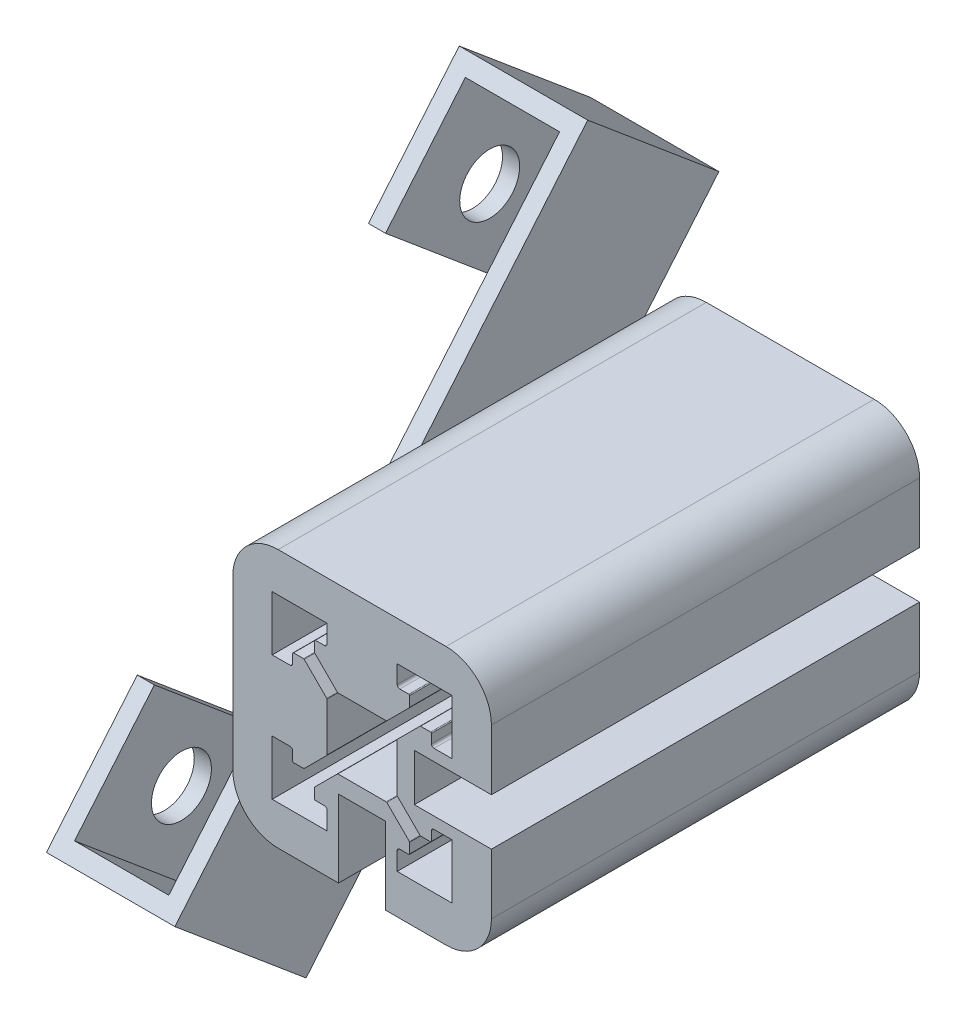
SolidWorks part; units mm, degrees
ref_plane "Ön Düzlem" through (0, 0, 0) normal (0, 0, 1) x (1, 0, 0)
ref_plane "Üst Düzlem" through (0, 0, 0) normal (0, 1, 0) x (1, 0, 0)
ref_plane "Sağ Düzlem" through (0, 0, 0) normal (1, 0, 0) x (0, 0, -1)
sketch "Çizim6" plane through (0, 0, 0) normal (0, 0, 1) x (1, 0, 0)
  line L5 (-115.3715, 18.9738) -> (-110.3715, 18.9738)
  line L6 (-115.3715, 13.4738) -> (-110.3715, 13.4738)
  line L64 (-135.0715, 20.3238) -> (-133.8715, 20.3238)
  line L65 (-133.5715, 20.6238) -> (-133.5715, 21.6738)
  line L66 (-133.4715, 21.7738) -> (-132.3044, 21.7738)
  line L67 (-132.2336, 21.7445) -> (-129.6008, 19.1116)
  line L68 (-129.5715, 19.0409) -> (-129.5715, 13.4066)
  line L69 (-132.2336, 10.7031) -> (-129.6008, 13.3359)
  line L70 (-133.4715, 10.6738) -> (-132.3044, 10.6738)
  line L71 (-133.5715, 11.8238) -> (-133.5715, 10.7738)
  line L72 (-135.0715, 12.1238) -> (-133.8715, 12.1238)
  line L79 (-129.5715, 6.6238) -> (-129.5715, 7.8238)
  line L80 (-129.8715, 8.1238) -> (-130.9215, 8.1238)
  line L81 (-131.0215, 8.2238) -> (-131.0215, 9.3909)
  line L82 (-130.9922, 9.4616) -> (-128.3594, 12.0945)
  line L83 (-128.2887, 12.1238) -> (-122.6544, 12.1238)
  line L84 (-119.9508, 9.4616) -> (-122.5836, 12.0945)
  line L85 (-119.9215, 8.2238) -> (-119.9215, 9.3909)
  line L86 (-121.0715, 8.1238) -> (-120.0215, 8.1238)
  line L87 (-121.3715, 6.6238) -> (-121.3715, 7.8238)
  line L94 (-115.8715, 12.1238) -> (-117.0715, 12.1238)
  line L95 (-117.3715, 11.8238) -> (-117.3715, 10.7738)
  line L96 (-117.4715, 10.6738) -> (-118.6387, 10.6738)
  line L97 (-118.7094, 10.7031) -> (-121.3422, 13.3359)
  line L98 (-121.3715, 13.4066) -> (-121.3715, 19.0409)
  line L99 (-118.7094, 21.7445) -> (-121.3422, 19.1116)
  line L100 (-117.4715, 21.7738) -> (-118.6387, 21.7738)
  line L101 (-117.3715, 20.6238) -> (-117.3715, 21.6738)
  line L102 (-115.8715, 20.3238) -> (-117.0715, 20.3238)
  line L109 (-121.3715, 25.8238) -> (-121.3715, 24.6238)
  line L110 (-121.0715, 24.3238) -> (-120.0215, 24.3238)
  line L111 (-119.9215, 24.2238) -> (-119.9215, 23.0566)
  line L112 (-119.9508, 22.9859) -> (-122.5836, 20.3531)
  line L113 (-122.6544, 20.3238) -> (-128.2887, 20.3238)
  line L114 (-130.9922, 22.9859) -> (-128.3594, 20.3531)
  line L115 (-131.0215, 24.2238) -> (-131.0215, 23.0566)
  line L116 (-129.8715, 24.3238) -> (-130.9215, 24.3238)
  line L117 (-129.5715, 25.8238) -> (-129.5715, 24.6238)
  line L122 (-119.3715, 18.9738) -> (-115.3715, 18.9738)
  line L123 (-119.3715, 13.4738) -> (-115.3715, 13.4738)
  line L126 (-119.3715, 18.9738) -> (-119.3715, 13.4738)
  line L128 (-122.7215, 10.1238) -> (-122.7215, 6.1238)
  line L129 (-122.7215, 10.1238) -> (-128.2215, 10.1238)
  line L130 (-128.2215, 10.1238) -> (-128.2215, 6.1238)
  line L142 (-135.0715, 20.3238) -> (-135.8715, 20.3238)
  line L143 (-135.0715, 12.1238) -> (-135.5715, 12.1238)
  line L144 (-129.5715, 6.6238) -> (-129.5715, 6.1238)
  line L145 (-129.5715, 25.8238) -> (-129.5715, 26.6238)
  line L146 (-121.3715, 25.8238) -> (-121.3715, 26.3238)
  line L147 (-115.8715, 20.3238) -> (-115.3715, 20.3238)
  line L148 (-115.8715, 12.1238) -> (-115.3715, 12.1238)
  line L149 (-121.3715, 6.6238) -> (-121.3715, 6.1238)
  line L150 (-135.2715, 31.3238) -> (-130.0215, 31.3238)
  line L151 (-130.0215, 31.3238) -> (-128.2215, 31.3238)
  line L152 (-125.4715, 31.3238) -> (-125.4715, 31.3238)
  line L153 (-125.4715, 31.3238) -> (-125.4715, 31.3238)
  line L154 (-125.4715, 31.3238) -> (-125.4715, 31.3238)
  line L155 (-120.9215, 31.3238) -> (-122.7215, 31.3238)
  line L156 (-120.9215, 31.3238) -> (-115.6715, 31.3238)
  line L157 (-110.3715, 20.7738) -> (-110.3715, 26.0238)
  line L158 (-110.3715, 20.7738) -> (-110.3715, 18.9738)
  line L159 (-110.3715, 16.2238) -> (-110.3715, 16.2238)
  line L160 (-110.3715, 16.2238) -> (-110.3715, 16.2238)
  line L161 (-110.3715, 16.2238) -> (-110.3715, 16.2238)
  line L162 (-110.3715, 11.6738) -> (-110.3715, 13.4738)
  line L163 (-110.3715, 6.4238) -> (-110.3715, 11.6738)
  line L164 (-120.9215, 1.1238) -> (-115.6715, 1.1238)
  line L165 (-120.9215, 1.1238) -> (-122.7215, 1.1238)
  line L166 (-125.4715, 1.1238) -> (-125.4715, 1.1238)
  line L167 (-125.4715, 1.1238) -> (-125.4715, 1.1238)
  line L168 (-125.4715, 1.1238) -> (-125.4715, 1.1238)
  line L169 (-130.0215, 1.1238) -> (-128.2215, 1.1238)
  line L170 (-135.2715, 1.1238) -> (-130.0215, 1.1238)
  line L171 (-140.5715, 6.4238) -> (-140.5715, 11.6738)
  line L172 (-140.5715, 11.6738) -> (-140.5715, 16.2238)
  line L173 (-140.5715, 16.2238) -> (-140.5715, 16.2238)
  line L174 (-140.5715, 16.2238) -> (-140.5715, 16.2238)
  line L175 (-140.5715, 16.2238) -> (-140.5715, 16.2238)
  line L176 (-140.5715, 20.7738) -> (-140.5715, 16.2238)
  line L177 (-140.5715, 20.7738) -> (-140.5715, 26.0238)
  line L178 (-135.5715, 20.7738) -> (-135.5715, 26.0238) construction
  line L179 (-135.2715, 26.3238) -> (-130.0215, 26.3238) construction
  line L180 (-115.3715, 20.7738) -> (-115.3715, 26.0238) construction
  line L181 (-120.9215, 26.3238) -> (-115.6715, 26.3238) construction
  line L182 (-115.3715, 20.7738) -> (-115.3715, 18.9738) construction
  line L183 (-115.3715, 6.4238) -> (-115.3715, 11.6738) construction
  line L184 (-120.9215, 6.1238) -> (-115.6715, 6.1238) construction
  line L185 (-115.3715, 11.6738) -> (-115.3715, 13.4738) construction
  line L186 (-120.9215, 6.1238) -> (-122.7215, 6.1238) construction
  line L187 (-120.9215, 26.3238) -> (-122.7215, 26.3238) construction
  line L188 (-130.0215, 26.3238) -> (-128.2215, 26.3238) construction
  line L189 (-135.5715, 20.7738) -> (-135.5715, 18.9738) construction
  line L190 (-135.5715, 11.6738) -> (-135.5715, 13.4738) construction
  line L191 (-135.5715, 6.4238) -> (-135.5715, 11.6738) construction
  line L192 (-135.2715, 6.1238) -> (-130.0215, 6.1238) construction
  line L193 (-130.0215, 6.1238) -> (-128.2215, 6.1238) construction
  line L194 (-122.7215, 6.1238) -> (-122.7215, 1.1238)
  line L195 (-128.2215, 6.1238) -> (-128.2215, 1.1238)
  line L196 (-135.8715, 20.3238) -> (-135.9715, 20.3238)
  line L197 (-135.9715, 20.2238) -> (-135.9715, 26.7238) construction
  line L198 (-122.7215, 31.3238) -> (-128.2215, 31.3238)
  line L204 (-110.3715, 20.7738) -> (-110.3715, 16.2238) construction
  line L205 (-110.3715, 11.6738) -> (-110.3715, 16.2238) construction
  line L206 (-120.9215, 31.3238) -> (-125.4715, 31.3238) construction
  line L207 (-130.0215, 31.3238) -> (-125.4715, 31.3238) construction
  line L208 (-120.9215, 1.1238) -> (-125.4715, 1.1238) construction
  line L209 (-130.0215, 1.1238) -> (-125.4715, 1.1238) construction
  line L210 (-131.5715, 13.4738) -> (-135.5715, 13.4738) [skipped]
  line L211 (-131.5715, 13.4738) -> (-135.5715, 13.4738) construction
  line L212 (-131.5715, 13.4738) -> (-131.5715, 18.9738) [skipped]
  line L213 (-131.5715, 13.4738) -> (-131.5715, 18.9738) construction
  line L214 (-131.5715, 18.9738) -> (-135.5715, 18.9738) [skipped]
  line L215 (-131.5715, 18.9738) -> (-135.5715, 18.9738) construction
  line L216 (-129.5715, 26.6238) -> (-129.5715, 26.7238)
  line L217 (-135.9715, 26.7238) -> (-129.4715, 26.7238) construction
  line L218 (-114.9715, 26.7238) -> (-114.9715, 20.3238)
  line L219 (-121.3715, 26.7238) -> (-114.9715, 26.7238)
  line L220 (-114.9715, 5.7238) -> (-121.3715, 5.7238)
  line L221 (-114.9715, 12.1238) -> (-114.9715, 5.7238)
  line L222 (-135.9715, 5.7238) -> (-135.9715, 12.1238)
  line L223 (-129.5715, 5.7238) -> (-135.9715, 5.7238)
  line L224 (-121.3715, 6.1238) -> (-121.3715, 5.7238)
  line L225 (-115.3715, 12.1238) -> (-114.9715, 12.1238)
  line L226 (-129.5715, 6.1238) -> (-129.5715, 5.7238)
  line L227 (-135.9715, 20.3238) -> (-135.9715, 26.7238)
  line L228 (-135.9715, 26.7238) -> (-129.5715, 26.7238)
  line L229 (-135.5715, 12.1238) -> (-135.9715, 12.1238)
  line L230 (-121.3715, 26.3238) -> (-121.3715, 26.7238)
  line L231 (-115.3715, 20.3238) -> (-114.9715, 20.3238)
  line L240 (-121.4715, 25.8238) -> (-121.4715, 26.3238) construction
  line L241 (-121.4715, 25.8238) -> (-121.4715, 24.6238) construction
  line L242 (-121.0715, 24.2238) -> (-120.0215, 24.2238) construction
  line L243 (-120.0215, 24.2238) -> (-120.0215, 23.0566) construction
  line L244 (-120.0215, 23.0566) -> (-122.6544, 20.4238) construction
  line L245 (-122.6544, 20.4238) -> (-128.2887, 20.4238) construction
  line L246 (-130.9215, 23.0566) -> (-128.2887, 20.4238) construction
  line L247 (-130.9215, 24.2238) -> (-130.9215, 23.0566) construction
  line L248 (-129.8715, 24.2238) -> (-130.9215, 24.2238) construction
  line L249 (-129.4715, 25.8238) -> (-129.4715, 24.6238) construction
  line L250 (-129.4715, 25.8238) -> (-129.4715, 26.7238) construction
  line L251 (-135.8715, 26.6238) -> (-129.5715, 26.6238) construction
  line L252 (-135.8715, 20.3238) -> (-135.8715, 26.6238) construction
  line L253 (-135.0715, 20.2238) -> (-135.9715, 20.2238) construction
  line L254 (-135.0715, 20.2238) -> (-133.8715, 20.2238) construction
  line L255 (-133.4715, 20.6238) -> (-133.4715, 21.6738) construction
  line L256 (-133.4715, 21.6738) -> (-132.3044, 21.6738) construction
  line L257 (-132.3044, 21.6738) -> (-129.6715, 19.0409) construction
  line L258 (-129.6715, 19.0409) -> (-129.6715, 13.4066) construction
  line L259 (-132.3044, 10.7738) -> (-129.6715, 13.4066) construction
  line L260 (-133.4715, 10.7738) -> (-132.3044, 10.7738) construction
  line L261 (-133.4715, 11.8238) -> (-133.4715, 10.7738) construction
  line L262 (-135.0715, 12.2238) -> (-133.8715, 12.2238) construction
  line L263 (-135.0715, 12.2238) -> (-135.5715, 12.2238) construction
  line L264 (-128.2215, 22.3238) -> (-128.2215, 26.3238) [skipped]
  line L265 (-128.2215, 22.3238) -> (-128.2215, 26.3238) construction
  line L266 (-128.2215, 22.3238) -> (-122.7215, 22.3238) [skipped]
  line L267 (-128.2215, 22.3238) -> (-122.7215, 22.3238) construction
  line L268 (-122.7215, 22.3238) -> (-122.7215, 26.3238) [skipped]
  line L269 (-122.7215, 22.3238) -> (-122.7215, 26.3238) construction
  arc A46 (-133.8715, 20.3238) -> (-133.5715, 20.6238) centre (-133.8715, 20.6238) ccw
  arc A47 (-133.5715, 21.6738) -> (-133.4715, 21.7738) centre (-133.4715, 21.6738) cw
  arc A48 (-132.2336, 21.7445) -> (-132.3044, 21.7738) centre (-132.3044, 21.6738) ccw
  arc A49 (-129.5715, 19.0409) -> (-129.6008, 19.1116) centre (-129.6715, 19.0409) ccw
  arc A50 (-129.5715, 13.4066) -> (-129.6008, 13.3359) centre (-129.6715, 13.4066) cw
  arc A51 (-132.2336, 10.7031) -> (-132.3044, 10.6738) centre (-132.3044, 10.7738) cw
  arc A52 (-133.4715, 10.6738) -> (-133.5715, 10.7738) centre (-133.4715, 10.7738) cw
  arc A53 (-133.5715, 11.8238) -> (-133.8715, 12.1238) centre (-133.8715, 11.8238) ccw
  arc A57 (-129.5715, 7.8238) -> (-129.8715, 8.1238) centre (-129.8715, 7.8238) ccw
  arc A58 (-130.9215, 8.1238) -> (-131.0215, 8.2238) centre (-130.9215, 8.2238) cw
  arc A59 (-130.9922, 9.4616) -> (-131.0215, 9.3909) centre (-130.9215, 9.3909) ccw
  arc A60 (-128.2887, 12.1238) -> (-128.3594, 12.0945) centre (-128.2887, 12.0238) ccw
  arc A61 (-122.6544, 12.1238) -> (-122.5836, 12.0945) centre (-122.6544, 12.0238) cw
  arc A62 (-119.9508, 9.4616) -> (-119.9215, 9.3909) centre (-120.0215, 9.3909) cw
  arc A63 (-119.9215, 8.2238) -> (-120.0215, 8.1238) centre (-120.0215, 8.2238) cw
  arc A64 (-121.0715, 8.1238) -> (-121.3715, 7.8238) centre (-121.0715, 7.8238) ccw
  arc A68 (-117.0715, 12.1238) -> (-117.3715, 11.8238) centre (-117.0715, 11.8238) ccw
  arc A69 (-117.3715, 10.7738) -> (-117.4715, 10.6738) centre (-117.4715, 10.7738) cw
  arc A70 (-118.7094, 10.7031) -> (-118.6387, 10.6738) centre (-118.6387, 10.7738) ccw
  arc A71 (-121.3715, 13.4066) -> (-121.3422, 13.3359) centre (-121.2715, 13.4066) ccw
  arc A72 (-121.3715, 19.0409) -> (-121.3422, 19.1116) centre (-121.2715, 19.0409) cw
  arc A73 (-118.7094, 21.7445) -> (-118.6387, 21.7738) centre (-118.6387, 21.6738) cw
  arc A74 (-117.4715, 21.7738) -> (-117.3715, 21.6738) centre (-117.4715, 21.6738) cw
  arc A75 (-117.3715, 20.6238) -> (-117.0715, 20.3238) centre (-117.0715, 20.6238) ccw
  arc A79 (-121.3715, 24.6238) -> (-121.0715, 24.3238) centre (-121.0715, 24.6238) ccw
  arc A80 (-120.0215, 24.3238) -> (-119.9215, 24.2238) centre (-120.0215, 24.2238) cw
  arc A81 (-119.9508, 22.9859) -> (-119.9215, 23.0566) centre (-120.0215, 23.0566) ccw
  arc A82 (-122.6544, 20.3238) -> (-122.5836, 20.3531) centre (-122.6544, 20.4238) ccw
  arc A83 (-128.2887, 20.3238) -> (-128.3594, 20.3531) centre (-128.2887, 20.4238) cw
  arc A84 (-130.9922, 22.9859) -> (-131.0215, 23.0566) centre (-130.9215, 23.0566) cw
  arc A85 (-131.0215, 24.2238) -> (-130.9215, 24.3238) centre (-130.9215, 24.2238) cw
  arc A86 (-129.8715, 24.3238) -> (-129.5715, 24.6238) centre (-129.8715, 24.6238) ccw
  arc A89 (-110.3715, 26.0238) -> (-115.6715, 31.3238) centre (-115.6715, 26.0238) ccw
  arc A90 (-115.6715, 1.1238) -> (-110.3715, 6.4238) centre (-115.6715, 6.4238) ccw
  arc A91 (-135.2715, 1.1238) -> (-140.5715, 6.4238) centre (-135.2715, 6.4238) cw
  arc A92 (-140.5715, 26.0238) -> (-135.2715, 31.3238) centre (-135.2715, 26.0238) cw
  arc A93 (-135.5715, 26.0238) -> (-135.2715, 26.3238) centre (-135.2715, 26.0238) cw construction
  arc A94 (-115.3715, 26.0238) -> (-115.6715, 26.3238) centre (-115.6715, 26.0238) ccw construction
  arc A95 (-115.6715, 6.1238) -> (-115.3715, 6.4238) centre (-115.6715, 6.4238) ccw construction
  arc A96 (-135.2715, 6.1238) -> (-135.5715, 6.4238) centre (-135.2715, 6.4238) cw construction
  arc A98 (-133.4715, 10.7738) -> (-133.4715, 10.7738) centre (-133.4715, 10.7738) cw
  arc A99 (-132.3044, 10.7738) -> (-132.3044, 10.7738) centre (-132.3044, 10.7738) cw
  arc A100 (-129.6715, 13.4066) -> (-129.6715, 13.4066) centre (-129.6715, 13.4066) cw
  arc A101 (-129.6715, 19.0409) -> (-129.6715, 19.0409) centre (-129.6715, 19.0409) ccw
  arc A102 (-132.3044, 21.6738) -> (-132.3044, 21.6738) centre (-132.3044, 21.6738) ccw
  arc A103 (-133.4715, 21.6738) -> (-133.4715, 21.6738) centre (-133.4715, 21.6738) cw
  arc A106 (-130.9215, 24.2238) -> (-130.9215, 24.2238) centre (-130.9215, 24.2238) cw
  arc A107 (-130.9215, 23.0566) -> (-130.9215, 23.0566) centre (-130.9215, 23.0566) cw
  arc A108 (-128.2887, 20.4238) -> (-128.2887, 20.4238) centre (-128.2887, 20.4238) cw
  arc A109 (-122.6544, 20.4238) -> (-122.6544, 20.4238) centre (-122.6544, 20.4238) ccw
  arc A110 (-120.0215, 23.0566) -> (-120.0215, 23.0566) centre (-120.0215, 23.0566) ccw
  arc A111 (-120.0215, 24.2238) -> (-120.0215, 24.2238) centre (-120.0215, 24.2238) cw
  arc A113 (-121.4715, 24.6238) -> (-121.0715, 24.2238) centre (-121.0715, 24.6238) ccw construction
  arc A114 (-129.8715, 24.2238) -> (-129.4715, 24.6238) centre (-129.8715, 24.6238) ccw construction
  arc A115 (-133.8715, 20.2238) -> (-133.4715, 20.6238) centre (-133.8715, 20.6238) ccw construction
  arc A116 (-133.4715, 11.8238) -> (-133.8715, 12.2238) centre (-133.8715, 11.8238) ccw construction
  point P0 (-125.4715, 16.2238)
  point P123 (-125.4715, 16.2238)
  point P329 (-125.4715, 16.2238)
  dimension "D6" = 4
  dimension "D2" = 0.1
  dimension "D3" = 5
  dimension "D4" = 2.4
  dimension "D5" = 2.4
  dimension "D14" = 4
extrude "Yükseklik-Ekstrüzyon3" add sketch "Çizim6" along normal mid plane 50
sketch "Çizim8" plane through (-140.5715, 0, 0) normal (-1, 0, 0) x (0, 0, 1)
  line L0 (0, 0) -> (0, 36.5333) construction
  line L2 (23.2295, -11.4601) -> (-24.1045, 44.9504) construction
  line L3 (31.765, -6.075) -> (-16.4441, 51.3783)
  line L4 (31.765, -6.075) -> (16.4441, -18.9308)
  line L9 (-16.4441, 51.3783) -> (-31.765, 38.5226)
  line L10 (16.4441, -18.9308) -> (-31.765, 38.5226)
  line L11 (31.765, -6.075) -> (-31.765, 38.5226) construction
  line L12 (-16.4441, 51.3783) -> (16.4441, -18.9308) construction
  line L13 (25, 6.4238) -> (25, 26.0238) construction
  point P6 (0, 16.2238)
  point P7 (24.1045, -12.5029)
  point P9 (25, 16.2238)
  point P16 (-24.1045, 44.9504)
  line M12 (-25, 6.4238) -> (25, 6.4238)
  line M14 (25, 26.0238) -> (-25, 26.0238)
  dimension "D1" = 40
  dimension "D2" = 75
  dimension "D3" = 20
extrude "Yükseklik-Ekstrüzyon4" add sketch "Çizim8" along normal blind 15 contours L10 L3 L9 M12 | L10 L3 M14 M12 | L10 L4 L3 M14
sketch "Çizim11" plane through (-155.5715, 0, 0) normal (-1, 0, 0) x (0, 0, 1)
  line L0 (24.1045, -12.5029) -> (-24.1045, 44.9504) construction
  line L1 (31.765, -6.075) -> (16.4441, -18.9308) construction
  line L2 (-16.4441, 51.3783) -> (-31.765, 38.5226) construction
  circle A1 centre (17.9981, -5.2255) radius 3.5
  circle A2 centre (-17.9981, 37.673) radius 3.5
  point P12 (0, 16.2238)
  dimension "D1" = 56
  dimension "D3" = 7
  dimension "D2" = 28
extrude "Kes-Ekstrüzyon3" cut sketch "Çizim11" against normal blind 10 contours A2 | A1
sketch "Çizim12" plane through (0, 13.1311, 15.6491) normal (0, 0.6428, 0.766) x (1, 0, 0)
  line L0 (-155.5715, 22.3702) -> (-155.5715, 49.9281)
  line L1 (-153.5715, 47.9281) -> (-153.5715, 36.1491)
  line L2 (-153.5715, 36.1491) -> (-153.5715, 36.1491)
  line L3 (-153.5715, 36.1491) -> (-153.5715, -23.0719)
  line L4 (-153.5715, -23.0719) -> (-142.5715, -23.0719)
  line L5 (-142.5715, -23.0719) -> (-142.5715, -8.7559)
  line L6 (-142.5715, -8.7559) -> (-142.5715, 16.8301)
  line L7 (-142.5715, 16.8301) -> (-142.5715, 47.9281)
  line L8 (-142.5715, 47.9281) -> (-153.5715, 47.9281)
  line L12 (-155.5715, 49.9281) -> (-155.5715, -25.0719)
  line L13 (-155.5715, -25.0719) -> (-140.5715, -25.0719)
  line L14 (-140.5715, -25.0719) -> (-140.5715, -8.7559)
  line L15 (-140.5715, -8.7559) -> (-140.5715, 16.8301)
  line L16 (-140.5715, 16.8301) -> (-140.5715, 49.9281)
  line L17 (-140.5715, 49.9281) -> (-155.5715, 49.9281)
  line L22 (-155.5715, 49.9281) -> (-155.5715, -25.0719)
  line L23 (-155.5715, -25.0719) -> (-140.5715, -25.0719)
  line L24 (-140.5715, -25.0719) -> (-140.5715, -8.7559)
  line L25 (-140.5715, -8.7559) -> (-140.5715, 16.8301)
  line L26 (-140.5715, 16.8301) -> (-140.5715, 49.9281)
  line L27 (-140.5715, 49.9281) -> (-155.5715, 49.9281)
  line L39 (-155.5715, 49.9281) -> (-155.5715, 22.3702) construction
  dimension "D1" = 0
  dimension "D2" = 2
extrude "Kes-Ekstrüzyon4" cut sketch "Çizim12" against normal blind 16
sketch "Çizim13" plane through (-155.5715, 0, 0) normal (-1, 0, 0) x (0, 0, 1)
  line L10 (-21.159, 25.8828) -> (-5.8381, 38.7386)
  line L11 (5.8381, -6.291) -> (21.159, 6.5647)
  line L19 (-31.765, 38.5226) -> (16.4441, -18.9308)
  line L20 (16.4441, -18.9308) -> (31.765, -6.075)
  line L21 (31.765, -6.075) -> (-16.4441, 51.3783)
  line L22 (-16.4441, 51.3783) -> (-31.765, 38.5226)
  line L23 (-31.765, 38.5226) -> (16.4441, -18.9308)
  line L24 (16.4441, -18.9308) -> (31.765, -6.075)
  line L25 (31.765, -6.075) -> (-16.4441, 51.3783)
  line L26 (-16.4441, 51.3783) -> (-31.765, 38.5226)
  point P8 (7.6604, 22.6516)
  dimension "D1" = 0
  dimension "D2" = 42
  dimension "D3" = 21
extrude "Kes-Ekstrüzyon5" cut sketch "Çizim13" against normal up to surface (13 mm away)
